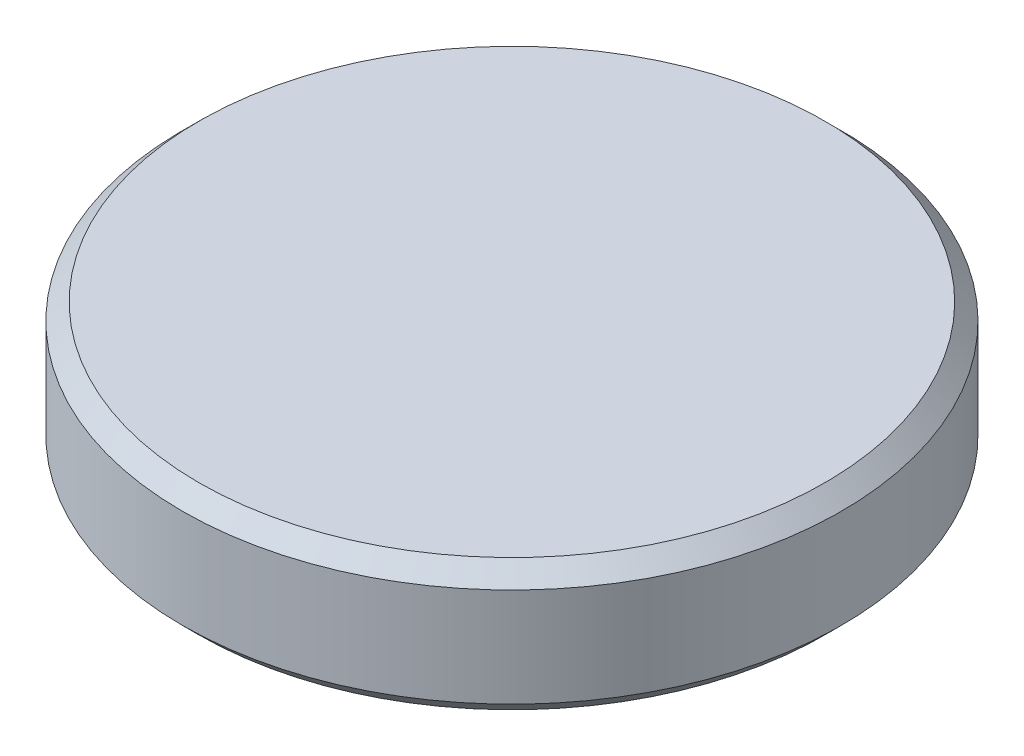
SolidWorks part; units mm, degrees
material "ﾒﾗﾐﾝ樹脂"
ref_plane "正面" through (0, 0, 0) normal (0, 0, 1) x (1, 0, 0)
ref_plane "平面" through (0, 0, 0) normal (0, 1, 0) x (1, 0, 0)
ref_plane "右側面" through (0, 0, 0) normal (1, 0, 0) x (0, 0, -1)
sketch "ｽｹｯﾁ1" plane through (0, 0, 0) normal (0, 1, 0) x (1, 0, 0)
  circle A0 centre (0, 0) radius 5
extrude "ﾎﾞｽ - 押し出し1" add sketch "ｽｹｯﾁ1" along normal blind 2
chamfer "面取り1" distance 0.25 angle 45 2 edges at (0, 0, 5) (0, 2, 5)
